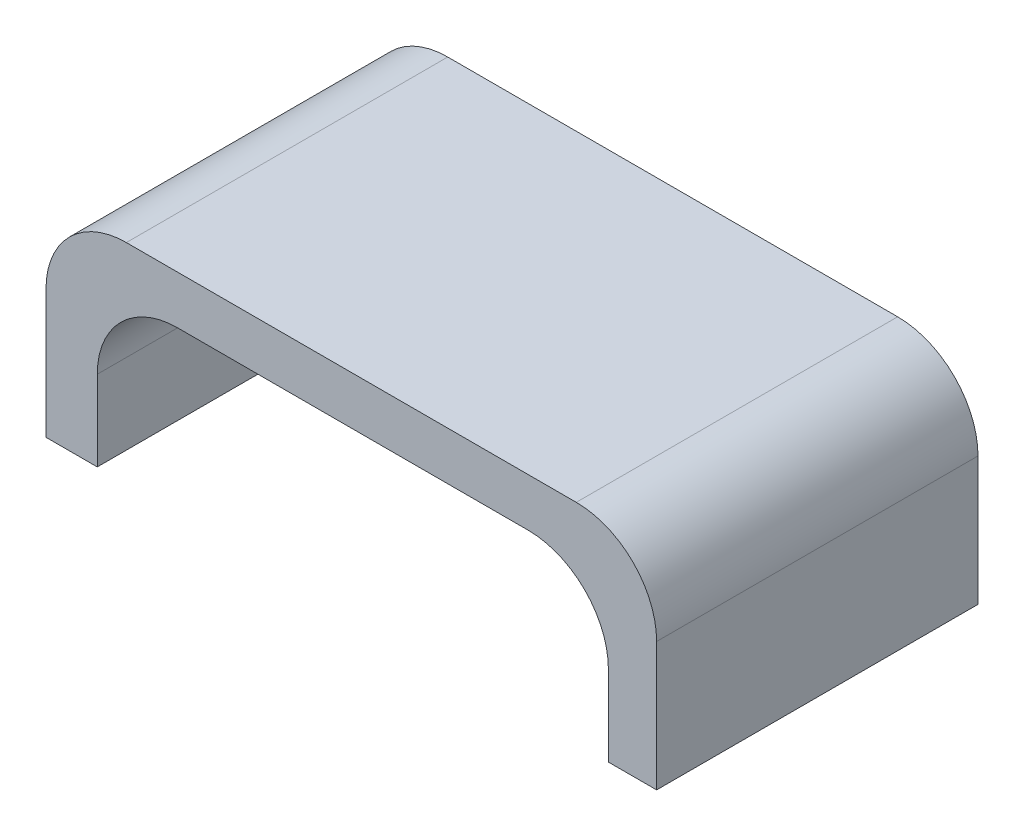
SolidWorks part; units mm, degrees
ref_plane "Front" through (0, 0, 0) normal (0, 0, 1) x (1, 0, 0)
ref_plane "Top" through (0, 0, 0) normal (0, 1, 0) x (1, 0, 0)
ref_plane "Right" through (0, 0, 0) normal (1, 0, 0) x (0, 0, -1)
sketch "草图1" plane through (0, 0, 0) normal (0, 0, 1) x (1, 0, 0)
  line L0 (0, 0) -> (0, 52.472) construction
  line L2 (-38, 14.0053) -> (-38, 20.0095)
  line L4 (38, 14) -> (38, 20)
  line L11 (38, 14) -> (32, 14)
  line L12 (28, 40) -> (-28, 40)
  line L14 (38, 20) -> (38, 30)
  line L15 (-38, 30) -> (-38, 20.0095)
  line L17 (32, 14) -> (32, 24)
  line L19 (22, 34) -> (-21.6161, 34)
  line L21 (-38, 14.0053) -> (-31.6161, 14.0053)
  line L22 (-31.6161, 14.0053) -> (-31.6161, 24)
  arc A0 (-31.6161, 24) -> (-21.6161, 34) centre (-21.6161, 24) cw
  arc A1 (22, 34) -> (32, 24) centre (22, 24) cw
  arc A2 (-28, 40) -> (-38, 30) centre (-28, 30) ccw
  arc A3 (38, 30) -> (28, 40) centre (28, 30) ccw
  point P23 (38, 40)
  dimension "D7" = 10
  dimension "D8" = 10
  dimension "D1" = 76
  dimension "D2" = 38
  dimension "D3" = 6
  dimension "D4" = 6
  dimension "D5" = 6
  dimension "D6" = 20
extrude "凸台-拉伸1" add sketch "草图1" along normal blind 40
